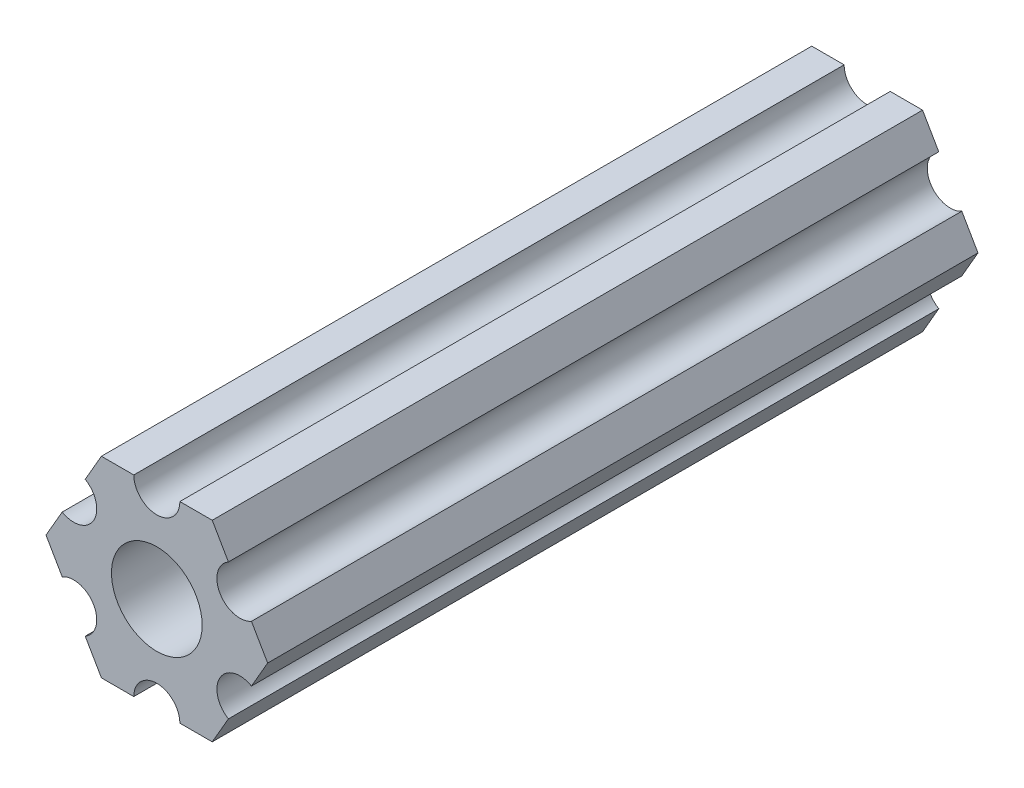
SolidWorks part; units mm, degrees
material "Churro - 6005A-T61"
ref_plane "Plano frontal" through (0, 0, 0) normal (0, 0, 1) x (1, 0, 0)
ref_plane "Plano superior" through (0, 0, 0) normal (0, 1, 0) x (1, 0, 0)
ref_plane "Plano direito" through (0, 0, 0) normal (1, 0, 0) x (0, 0, -1)
sketch "Esboço1" plane through (0, 0, 0) normal (0, 0, 1) x (1, 0, 0)
  line L1 (3.6662, 6.35) -> (-3.6662, 6.35)
  line L2 (-3.6662, 6.35) -> (-7.3323, 0)
  line L3 (-7.3323, 0) -> (-3.6662, -6.35)
  line L4 (-3.6662, -6.35) -> (3.6662, -6.35)
  line L5 (3.6662, -6.35) -> (7.3323, 0)
  line L6 (7.3323, 0) -> (3.6662, 6.35)
  circle A0 centre (0, 0) radius 6.35 construction
  circle A1 centre (0, 0) radius 3
  circle A2 centre (0, 6.35) radius 1.524
  circle A3 centre (5.4993, 3.175) radius 1.524
  circle A4 centre (5.4993, -3.175) radius 1.524
  circle A5 centre (0, -6.35) radius 1.524
  circle A6 centre (-5.4993, -3.175) radius 1.524
  circle A7 centre (-5.4993, 3.175) radius 1.524
  point P24 (0, 0)
  dimension "D1" = 12.7
  dimension "D2" = 6
  dimension "D3" = 3.048
  dimension "D4" = 6
extrude "Ressalto-extrusão1" add sketch "Esboço1" along normal blind 47 contours A7 L2 L3 A6 L4 A5 L5 A4 L6 A3 L1 A2 A1
